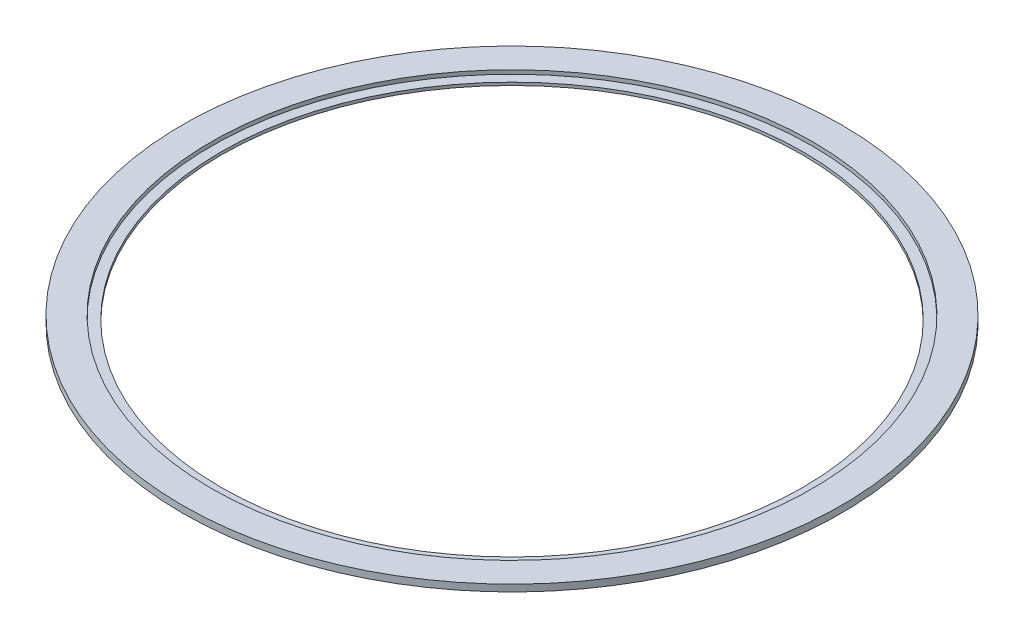
SolidWorks part; units mm, degrees
material "2014-O"
ref_plane "正面" through (0, 0, 0) normal (0, 0, 1) x (1, 0, 0)
ref_plane "平面" through (0, 0, 0) normal (0, 1, 0) x (1, 0, 0)
ref_plane "右側面" through (0, 0, 0) normal (1, 0, 0) x (0, 0, -1)
sketch "ｽｹｯﾁ1" plane through (0, 0, 0) normal (0, 1, 0) x (1, 0, 0)
  circle A0 centre (0, 0) radius 160
  circle A1 centre (0, 0) radius 150
  dimension "D1" = 320
  dimension "D2" = 300
extrude "ﾎﾞｽ - 押し出し1" add sketch "ｽｹｯﾁ1" along normal blind 1.5
sketch "ｽｹｯﾁ2" plane through (0, 1.5, 0) normal (0, 1, 0) x (1, 0, 0)
  circle A0 centre (0, 0) radius 152.5
  circle A1 centre (0, 0) radius 160
  dimension "D1" = 305
extrude "ﾎﾞｽ - 押し出し2" add sketch "ｽｹｯﾁ2" along normal blind 2
sketch "ｽｹｯﾁ3" plane through (0, 3.5, 0) normal (0, 1, 0) x (1, 0, 0)
  circle A0 centre (0, 0) radius 170
  circle A1 centre (0, 0) radius 160
  dimension "D1" = 340
extrude "ﾎﾞｽ - 押し出し3" add sketch "ｽｹｯﾁ3" against normal up to surface (3.5 mm away) up to face at (0, 0, 160)
sketch "ｽｹｯﾁ4" plane through (0, 3.5, 0) normal (0, 1, 0) x (1, 0, 0)
  circle A0 centre (0, 0) radius 155
  circle A1 centre (0, 0) radius 152.5
  dimension "D1" = 310
extrude "ｶｯﾄ - 押し出し1" cut sketch "ｽｹｯﾁ4" against normal blind 2
